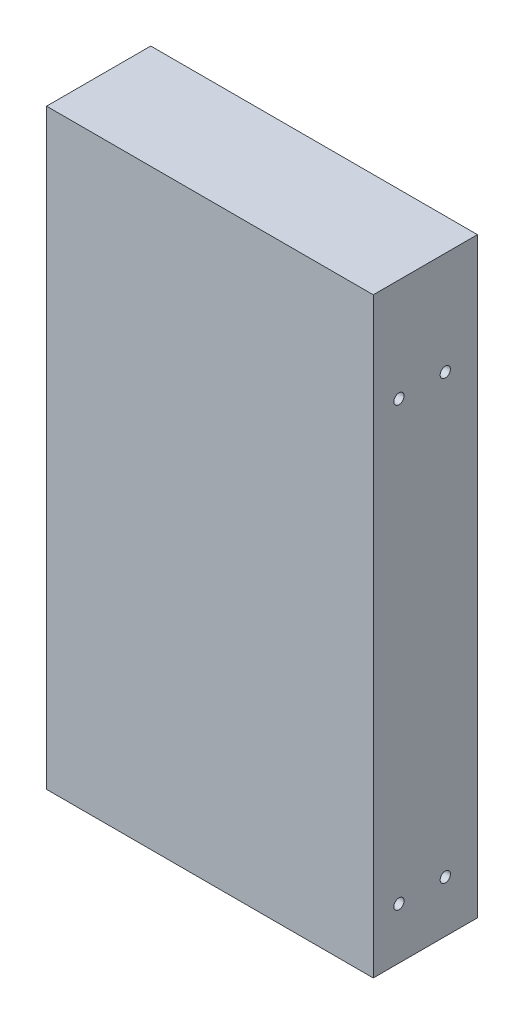
SolidWorks part; units mm, degrees
ref_plane "Alzado" through (0, 0, 0) normal (0, 0, 1) x (1, 0, 0)
ref_plane "Planta" through (0, 0, 0) normal (0, 1, 0) x (1, 0, 0)
ref_plane "Vista lateral" through (0, 0, 0) normal (1, 0, 0) x (0, 0, -1)
sketch "Croquis1" plane through (0, 0, 0) normal (0, 0, 1) x (1, 0, 0)
  line L1 (0, 0) -> (-127, 0)
  line L2 (0, 0) -> (0, 230)
  line L3 (0, 230) -> (-127, 230)
  line L4 (-127, 0) -> (-127, 230)
  dimension "D1" = 230
  dimension "D2" = 127
extrude "Saliente-Extruir2" add sketch "Croquis1" along normal blind 40.5 contours L3 L4 L1 L2
sketch "Croquis3" plane through (0, 0, 0) normal (1, 0, 0) x (0, 0, -1)
  line L0 (-12.5, 190) -> (-12.5, -76.6149) construction
  line L1 (-40.5, 230) -> (0, 230) construction
  line L2 (-12.5, 20) -> (-36.8198, 20) construction
  line L3 (-21.5, 20) -> (-21.5, 26.2208) construction
  line L4 (0, 0) -> (0, 230) construction
  circle A0 centre (-12.5, 190) radius 2
  circle A1 centre (-12.5, 20) radius 2
  circle A2 centre (-30.5, 190) radius 2
  circle A3 centre (-30.5, 20) radius 2
  dimension "D1" = 4
  dimension "D2" = 4
  dimension "D3" = 170
  dimension "D4" = 40
  dimension "D5" = 9
  dimension "D6" = 12.5
extrude "Cortar-Extruir1" cut sketch "Croquis3" against normal blind 10
